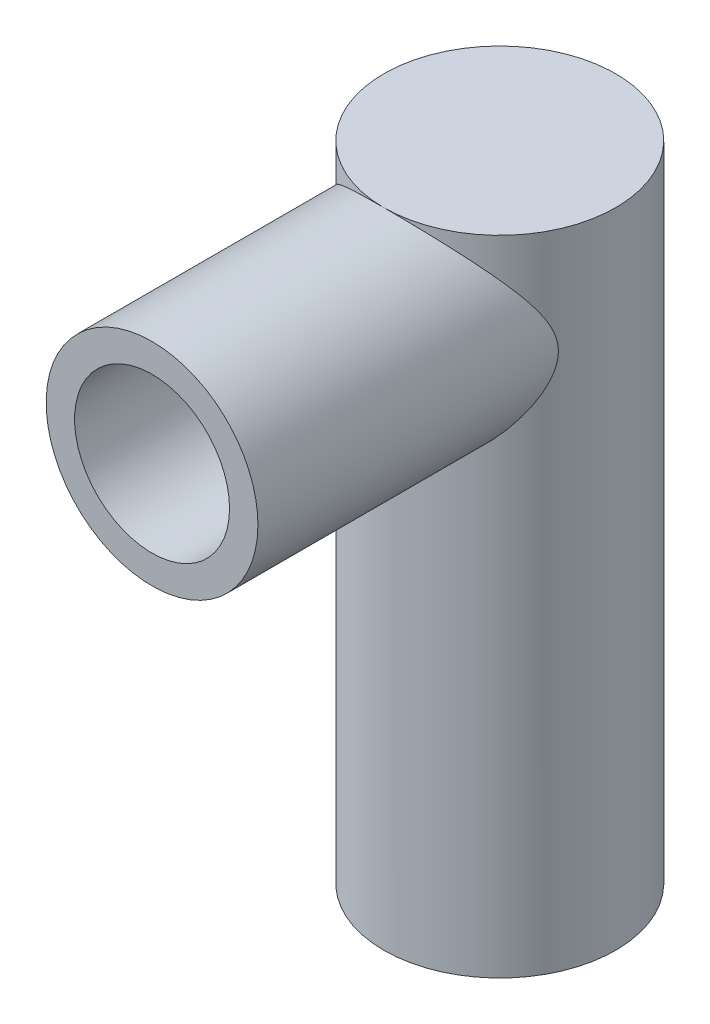
SolidWorks part; units mm, degrees
ref_plane "Front Plane" through (0, 0, 0) normal (0, 0, 1) x (1, 0, 0)
ref_plane "Top Plane" through (0, 0, 0) normal (0, 1, 0) x (1, 0, 0)
ref_plane "Right Plane" through (0, 0, 0) normal (1, 0, 0) x (0, 0, -1)
sketch "Sketch1" plane through (0, 0, 0) normal (0, 1, 0) x (1, 0, 0)
  circle A0 centre (0, 0) radius 15.3
  dimension "D1" = 30.6
extrude "Boss-Extrude1" add sketch "Sketch1" along normal blind 84.864
sketch "Sketch2" plane through (0, 0, 0) normal (0, 0, 1) x (1, 0, 0)
  line L0 (15.3, 84.864) -> (-15.3, 84.864) construction
  circle A0 centre (0, 70.894) radius 13.97
  dimension "D1" = 27.94
extrude "Boss-Extrude2" add sketch "Sketch2" along normal blind 57.15
sketch "Sketch3" plane through (0, 0, 57.15) normal (0, 0, 1) x (1, 0, 0)
  line L0 (0, 70.894) -> (0, 40.8389) construction
  line L1 (16.764, 70.894) -> (16.764, 40.8389)
  line L2 (-16.764, 70.894) -> (-16.764, 40.8389)
  arc A0 (16.764, 70.894) -> (-16.764, 70.894) centre (0, 70.894) ccw
  arc A1 (-16.764, 40.8389) -> (16.764, 40.8389) centre (0, 40.8389) ccw
  point P4 (0, 55.8664)
  dimension "D2" = 16.764
extrude "Boss-Extrude3" add sketch "Sketch3" along normal mid plane 5.08
sketch "Sketch4" plane through (0, 0, 59.69) normal (0, 0, 1) x (1, 0, 0)
  circle A0 centre (0, 40.8389) radius 10.2235
  dimension "D1" = 20.447
extrude "Cut-Extrude1" cut sketch "Sketch4" against normal blind 5.08
sketch "Sketch5" plane through (0, 0, 54.61) normal (0, 0, -1) x (-1, 0, 0)
  circle A0 centre (0, 40.8389) radius 14.2621
  circle A1 centre (0, 40.8389) radius 10.2235 construction
  circle A2 centre (0, 40.8389) radius 10.2235
  dimension "D1" = 28.5242
extrude "Boss-Extrude4" add sketch "Sketch5" along normal mid plane 38.1
sketch "Sketch6" plane through (0, 0, 0) normal (0, -1, 0) x (1, 0, 0)
  circle A0 centre (0, 0) radius 10.75
  dimension "D1" = 21.5
extrude "Cut-Extrude2" cut sketch "Sketch6" against normal blind 6.2
sketch "Sketch8" plane through (0, 0, 59.69) normal (0, 0, 1) x (1, 0, 0)
  line L2 (-16.764, 70.894) -> (-16.764, 40.8389)
  line L3 (16.764, 40.8389) -> (16.764, 70.894)
  line L4 (-16.764, 70.894) -> (-16.764, 40.8389)
  line L5 (16.764, 40.8389) -> (16.764, 70.894)
  circle A0 centre (0, 40.8389) radius 14.2621 construction
  circle A1 centre (0, 40.8389) radius 14.2621
  arc A2 (16.764, 70.894) -> (-16.764, 70.894) centre (0, 70.894) ccw
  arc A3 (-16.764, 40.8389) -> (16.764, 40.8389) centre (0, 40.8389) ccw
  arc A4 (16.764, 70.894) -> (-16.764, 70.894) centre (0, 70.894) ccw
  arc A5 (-16.764, 40.8389) -> (16.764, 40.8389) centre (0, 40.8389) ccw
  dimension "D1" = 0
extrude "Cut-Extrude5" cut sketch "Sketch8" against normal blind 10.16
sketch "Sketch10" plane through (0, 0, 49.53) normal (0, 0, 1) x (1, 0, 0)
  circle A1 centre (0, 70.894) radius 13.97
  circle A2 centre (0, 70.894) radius 13.97
  dimension "D1" = 0
extrude "Boss-Extrude5" add sketch "Sketch10" along normal up to surface (24.13 mm away)
sketch "Sketch11" plane through (0, 0, 73.66) normal (0, 0, 1) x (1, 0, 0)
  circle A0 centre (0, 70.894) radius 10.2235
  dimension "D1" = 20.447
extrude "Cut-Extrude7" cut sketch "Sketch11" against normal blind 41.91
sketch "Sketch12" plane through (0, 0, 31.75) normal (0, 0, 1) x (1, 0, 0)
  circle A0 centre (0, 70.894) radius 6.35
  dimension "D1" = 12.7
sketch "Sketch13" plane through (0, 0, 73.66) normal (0, 0, 1) x (1, 0, 0)
  circle A0 centre (0, 40.8389) radius 10.2235 construction
  circle A1 centre (0, 40.8389) radius 14.2621
  circle A2 centre (0, 40.8389) radius 14.2621
  circle A3 centre (0, 40.8389) radius 10.2235
  dimension "D1" = 0
extrude "Cut-Extrude9" cut sketch "Sketch13" against normal blind 41.91
sketch "Sketch14" plane through (0, 0, 31.75) normal (0, 0, 1) x (1, 0, 0)
  circle A1 centre (0, 70.894) radius 10.2235
  circle A2 centre (0, 70.894) radius 10.2235
  dimension "D1" = 0
sketch "Sketch16" plane through (0, 0, 73.66) normal (0, 0, 1) x (1, 0, 0)
  circle A0 centre (0, 70.894) radius 10.2235 construction
  circle A1 centre (0, 70.894) radius 13.97
  circle A2 centre (0, 70.894) radius 13.97
  circle A3 centre (0, 70.894) radius 10.2235
  dimension "D1" = 0
extrude "Cut-Extrude10" cut sketch "Sketch16" against normal blind 27.7812
sketch "Sketch17" plane through (0, 0, 31.75) normal (0, 0, 1) x (1, 0, 0)
  circle A1 centre (0, 70.894) radius 10.2235
  circle A2 centre (0, 70.894) radius 10.2235
  dimension "D1" = 0
extrude "Cut-Extrude11" cut sketch "Sketch17" against normal blind 27.686
sketch "Sketch18" plane through (0, 0, 4.064) normal (0, 0, 1) x (1, 0, 0)
  circle A0 centre (0, 70.894) radius 6.35
  dimension "D1" = 12.7
extrude "Cut-Extrude12" cut sketch "Sketch18" against normal blind 111.506
